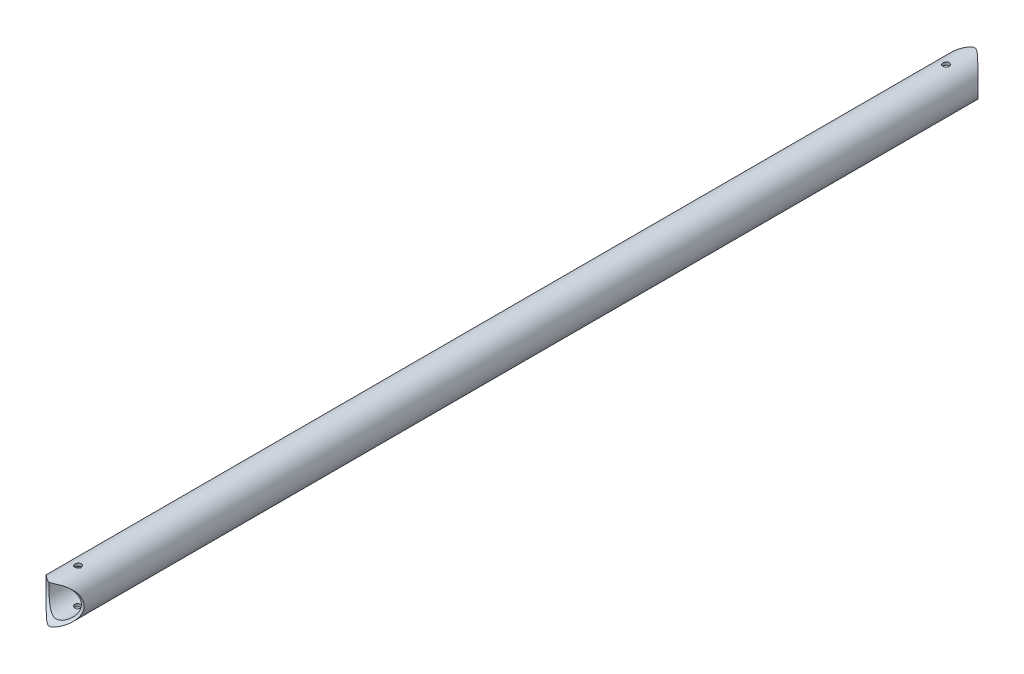
SolidWorks part; units mm, degrees
ref_plane "Front" through (0, 0, 0) normal (0, 0, 1) x (1, 0, 0)
ref_plane "Top" through (0, 0, 0) normal (0, 1, 0) x (1, 0, 0)
ref_plane "Right" through (0, 0, 0) normal (1, 0, 0) x (0, 0, -1)
sketch "Sketch1" plane through (0, 0, 0) normal (0, 0, 1) x (1, 0, 0)
  circle A0 centre (0, 0) radius 9.36
  circle A1 centre (0, 0) radius 7.99
extrude "Extrude1" add sketch "Sketch1" along normal blind 457.2
sketch "Sketch2" plane through (0, 0, 0) normal (1, 0, 0) x (0, 0, -1)
  circle A0 centre (0, 0) radius 9.525
extrude "Cut-Extrude1" cut sketch "Sketch2" against normal through all and the other way through all
sketch "Sketch3" plane through (0, 0, 0) normal (1, 0, 0) x (0, 0, -1)
  line L0 (-457.2, 0) -> (-9.5246, 0) construction
  circle A0 centre (-457.2, 0) radius 9.525
extrude "Cut-Extrude2" cut sketch "Sketch3" against normal through all and the other way through all
sketch "Sketch5" plane through (0, 0, 0) normal (0, 1, 0) x (1, 0, 0)
  line L0 (0, -447.6754) -> (0, -9.5246) construction
  circle A0 centre (0, -441.33) radius 1.55
  circle A1 centre (0, -15.88) radius 1.55
extrude "Cut-Extrude3" cut sketch "Sketch5" against normal through all and the other way through all
